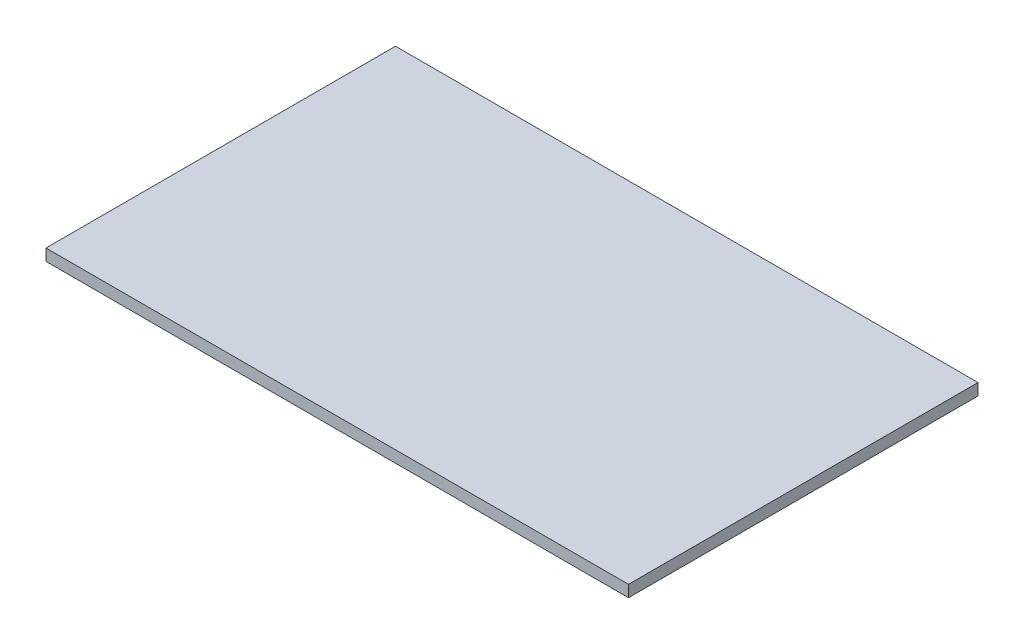
SolidWorks part; units mm, degrees
ref_plane "Front Plane" through (0, 0, 0) normal (0, 0, 1) x (1, 0, 0)
ref_plane "Top Plane" through (0, 0, 0) normal (0, 1, 0) x (1, 0, 0)
ref_plane "Right Plane" through (0, 0, 0) normal (1, 0, 0) x (0, 0, -1)
sketch "Sketch2" plane through (0, 0, 0) normal (0, 1, 0) x (1, 0, 0)
  line L1 (-29.5, 15) -> (29.5, 15)
  line L2 (-32.5, 12) -> (-32.5, -12)
  line L3 (-29.5, -15) -> (29.5, -15)
  line L4 (32.5, 12) -> (32.5, -12)
  line L5 (-32.5, 15) -> (32.5, -15) construction
  line L6 (-32.5, -15) -> (32.5, 15) construction
  arc A0 (29.5, 15) -> (32.5, 12) centre (29.5, 12) cw
  arc A1 (29.5, -15) -> (32.5, -12) centre (29.5, -12) ccw
  arc A2 (-32.5, -12) -> (-29.5, -15) centre (-29.5, -12) ccw
  arc A3 (-29.5, 15) -> (-32.5, 12) centre (-29.5, 12) ccw
  point P0 (0, 0)
  dimension "D3" = 3
  dimension "D1" = 65
  dimension "D2" = 30
extrude "Boss-Extrude1" add sketch "Sketch2" along normal blind 2
sketch "Sketch3" plane through (0, 2, 0) normal (0, 1, 0) x (1, 0, 0)
  line L0 (-29, 11.5) -> (-29, -11.5) construction
  line L1 (-32.5, 12) -> (-32.5, -12) construction
  line L2 (29.5, 15) -> (-29.5, 15) construction
  line L3 (0, 23.9085) -> (0, -18.0088) construction
  line L4 (-29.5, -15) -> (29.5, -15) construction
  circle A0 centre (-29, 11.5) radius 1.25
  circle A11 centre (-29, -11.5) radius 1.25
  circle A12 centre (29, -11.5) radius 1.25
  circle A13 centre (29, 11.5) radius 1.25
  dimension "D1" = 2.5
  dimension "D5" = 3.5
  dimension "D6" = 3.5
  dimension "D3" = 3.5
  dimension "D2" = 2
extrude "Boss-Extrude2" [suppressed] add sketch "Sketch3" along normal blind 15
sketch "Sketch4" plane through (0, 0, 0) normal (0, 1, 0) x (1, 0, 0)
  line L1 (-50, 30) -> (50, 30)
  line L2 (-50, 30) -> (-50, -30)
  line L3 (-50, -30) -> (50, -30)
  line L4 (50, 30) -> (50, -30)
  line L5 (-50, 30) -> (50, -30) construction
  line L6 (-50, -30) -> (50, 30) construction
  point P0 (0, 0)
  dimension "D1" = 100
  dimension "D2" = 60
extrude "Boss-Extrude3" add sketch "Sketch4" along normal up to surface (2 mm away) up to face at (0, 2, 0)
